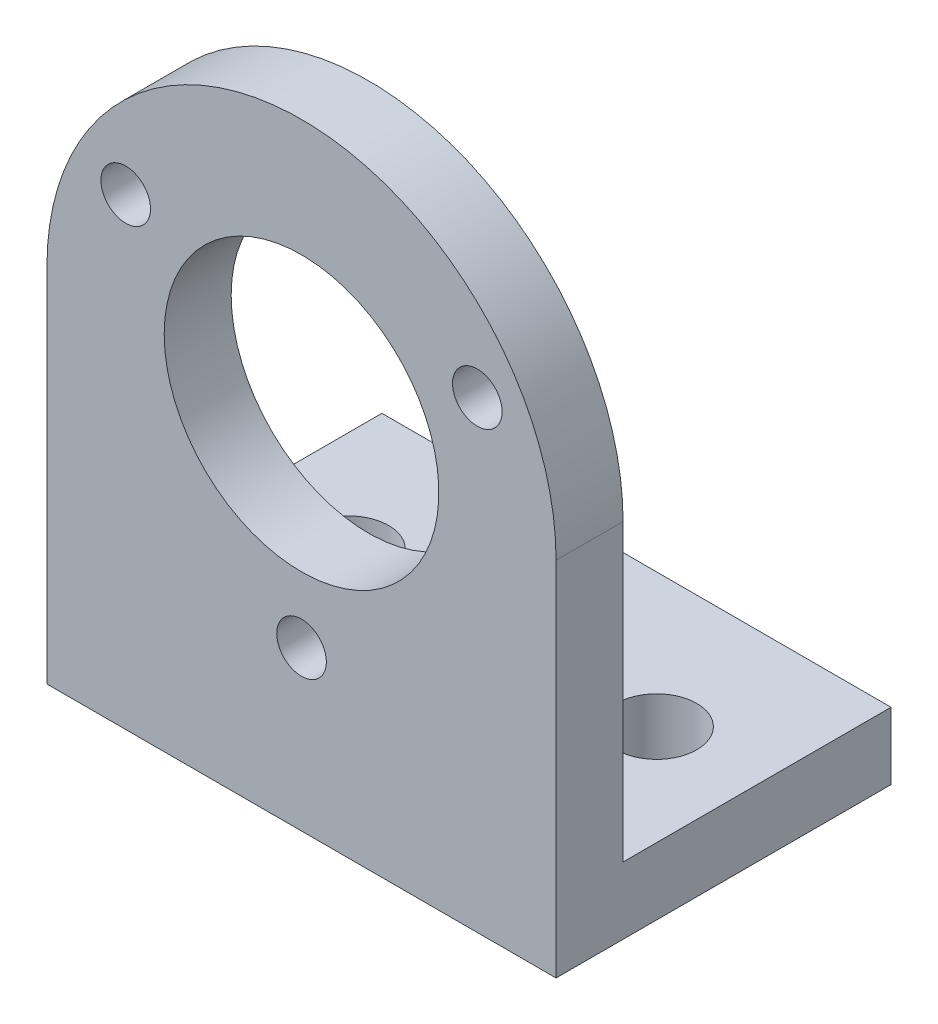
SolidWorks part; units mm, degrees
material "Aluminum Bronze"
ref_plane "Front Plane" through (0, 0, 0) normal (0, 0, 1) x (1, 0, 0)
ref_plane "Top Plane" through (0, 0, 0) normal (0, 1, 0) x (1, 0, 0)
ref_plane "Right Plane" through (0, 0, 0) normal (1, 0, 0) x (0, 0, -1)
sketch "Sketch1" plane through (0, 0, 0) normal (0, 0, 1) x (1, 0, 0)
  line L3 (-20.1587, 0) -> (-20.1587, -27)
  line L4 (-20.1587, -27) -> (17.8413, -27)
  line L5 (17.8413, -27) -> (17.8413, 0)
  arc A3 (17.8413, 0) -> (-20.1587, 0) centre (-1.1587, 0) ccw
  dimension "D1" = 19
  dimension "D2" = 27
extrude "Boss-Extrude1" add sketch "Sketch1" along normal blind 5
sketch "Sketch2" plane through (0, 0, 0) normal (0, 0, -1) x (-1, 0, 0)
  line L0 (1.1587, 0) -> (-20.9161, 12.7449) construction
  line L1 (1.1587, -15.15) -> (1.1587, 0) construction
  line L2 (1.1587, 0) -> (16.8914, 9.0832) construction
  line L3 (20.1587, -27) -> (-17.8413, -27) construction
  circle A8 centre (1.1587, 0) radius 10.25
  circle A9 centre (1.1587, 0) radius 15.15 construction
  circle A10 centre (1.1587, -15.15) radius 1.85
  circle A11 centre (-11.9615, 7.575) radius 1.85
  circle A12 centre (14.279, 7.575) radius 1.85
  dimension "D1" = 20.5
  dimension "D2" = 30.3
  dimension "D3" = 3.7
  dimension "D5" = 120
  dimension "D4" = 120
extrude "Cut-Extrude1" cut sketch "Sketch2" against normal through all
sketch "Sketch3" plane through (0, 0, 0) normal (0, 0, -1) x (-1, 0, 0)
  line L0 (20.1587, 0) -> (20.1587, -27) construction
  line L1 (-17.8413, -27) -> (20.1587, -27)
  line L2 (-17.8413, -27) -> (-17.8413, -22)
  line L3 (-17.8413, -22) -> (20.1587, -22)
  line L4 (20.1587, -27) -> (20.1587, -22)
  dimension "D1" = 5
extrude "Boss-Extrude2" add sketch "Sketch3" along normal blind 20
sketch "Sketch4" plane through (0, -22, 0) normal (0, 1, 0) x (1, 0, 0)
  line L0 (17.8413, 20) -> (17.8413, 0) construction
  line L1 (-20.1587, 20) -> (17.8413, 20) construction
  line L2 (17.8413, 0) -> (-20.1587, 0) construction
  line L3 (-20.1587, 20) -> (-20.1587, 0) construction
  circle A0 centre (10.3413, 10) radius 3
  circle A1 centre (-12.6587, 10) radius 3
  dimension "D1" = 6
  dimension "D2" = 6
  dimension "D3" = 10
  dimension "D4" = 10
  dimension "D5" = 7.5
  dimension "D6" = 7.5
extrude "Cut-Extrude2" cut sketch "Sketch4" against normal through all
